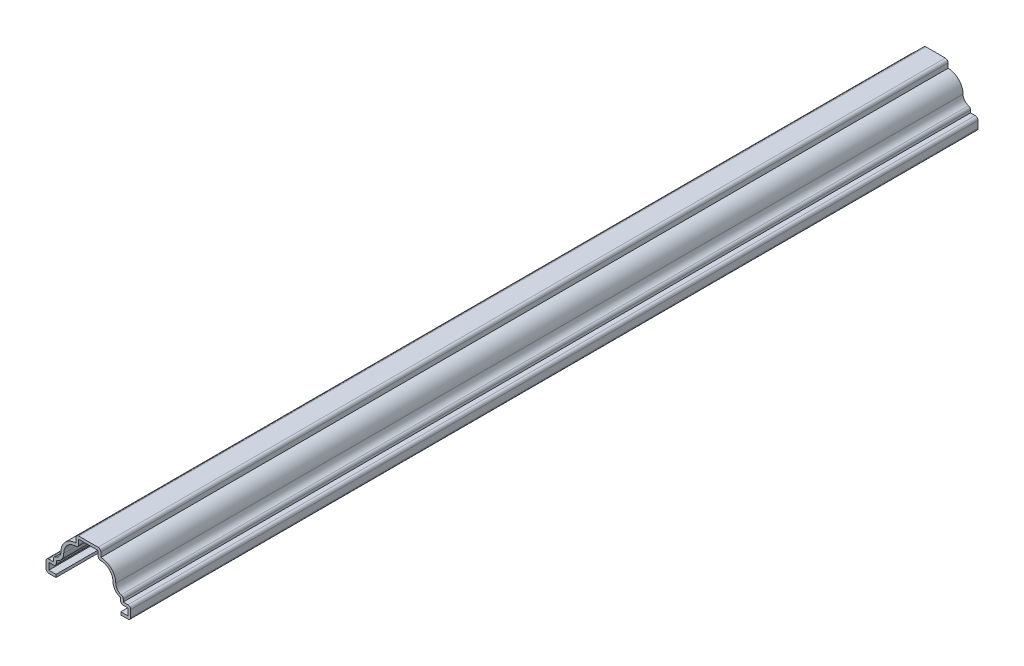
SolidWorks part; units mm, degrees
ref_plane "Front Plane" through (0, 0, 0) normal (0, 0, 1) x (1, 0, 0)
ref_plane "Top Plane" through (0, 0, 0) normal (0, 1, 0) x (1, 0, 0)
ref_plane "Right Plane" through (0, 0, 0) normal (1, 0, 0) x (0, 0, -1)
sketch "Sketch1" plane through (0, 0, 0) normal (0, 0, 1) x (1, 0, 0)
  line L0 (0, 0) -> (0, 15.0812) construction
  line L1 (3.9687, 15.0812) -> (-3.9687, 15.0812)
  line L2 (-3.9687, 15.0812) -> (-3.9687, 12.7)
  line L3 (3.9687, 15.0812) -> (3.9687, 12.7)
  line L4 (-11.1125, 5.5563) -> (-11.1125, 3.9688)
  line L5 (11.1125, 5.5563) -> (11.1125, 3.9688)
  line L6 (-11.1125, 3.9688) -> (-13.4937, 3.9688)
  line L7 (11.1125, 3.9688) -> (13.4937, 3.9688)
  line L8 (-13.4937, 3.9688) -> (-13.4937, 0)
  line L9 (13.4937, 3.9688) -> (13.4937, 0)
  line L10 (-13.4937, 0) -> (-10.3187, 0)
  line L11 (13.4937, 0) -> (10.3187, 0)
  arc A0 (-3.9687, 12.7) -> (-8.7312, 7.9375) centre (-3.9687, 7.9375) ccw
  arc A1 (3.9687, 12.7) -> (8.7312, 7.9375) centre (3.9687, 7.9375) cw
  arc A2 (-8.7312, 7.9375) -> (-11.1125, 5.5563) centre (-11.1125, 7.9375) cw
  arc A3 (8.7312, 7.9375) -> (11.1125, 5.5563) centre (11.1125, 7.9375) ccw
  point P23 (0, 19.3386)
  dimension "D9" = 4.7625
  dimension "D1" = 3.175
  dimension "D2" = 3.9688
  dimension "D3" = 1.5875
  dimension "D4" = 15.0812
  dimension "D5" = 7.1437
  dimension "D6" = 2.3813
  dimension "D7" = 7.1437
  dimension "D8" = 26.9875
extrude "Extrude-Thin1" add sketch "Sketch1" against normal blind 269.875 thin thin type one direction reverse wall 0.889
fillet "Fillet1" radius 0.889 12 edges at (13.4937, 3.9688, -134.9375) (13.4937, 0, -134.9375) (10.2235, 3.0798, -134.9375) (11.1125, 5.5563, -134.9375) (3.0797, 11.7076, -134.9375) (3.9687, 15.0812, -134.9375) (-3.9687, 15.0812, -134.9375) (-3.0797, 11.7076, -134.9375) (-10.2235, 3.0798, -134.9375) (-11.1125, 5.5562, -134.9375) (-13.4937, 0, -134.9375) (-13.4937, 3.9688, -134.9375)
